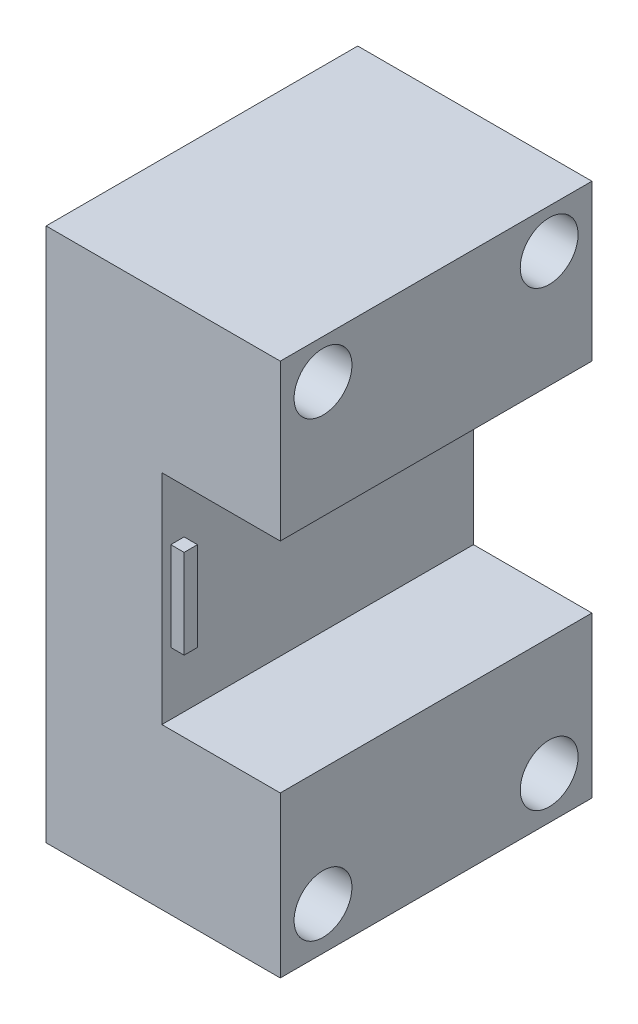
SolidWorks part; units mm, degrees
ref_plane "Front Plane" through (0, 0, 0) normal (0, 0, 1) x (1, 0, 0)
ref_plane "Top Plane" through (0, 0, 0) normal (0, 1, 0) x (1, 0, 0)
ref_plane "Right Plane" through (0, 0, 0) normal (1, 0, 0) x (0, 0, -1)
sketch "Sketch1" plane through (0, 0, 0) normal (0, 0, 1) x (1, 0, 0)
  line L0 (0, 0) -> (13, 0)
  line L7 (0, 60) -> (13, 60)
  line L9 (13, 60) -> (13, 0)
  line L10 (0, 60) -> (0, 0)
  point P4 (0, 0)
  point P6 (0, 0)
  dimension "D1" = 13
  dimension "D5" = 60
extrude "Boss-Extrude1" add sketch "Sketch1" against normal blind 35 contours L0 L9 L7 L10
sketch "Sketch3" plane through (13, 0, 0) normal (1, 0, 0) x (0, 0, -1)
  line L1 (1, 25) -> (2.5, 25)
  line L2 (1, 25) -> (1, 35)
  line L3 (1, 35) -> (2.5, 35)
  line L4 (2.5, 25) -> (2.5, 35)
  line L7 (0, 60) -> (0, 0) construction
  line L8 (35, 60) -> (0, 60) construction
  line L9 (35, 0) -> (0, 0) construction
  point P4 (8.1914, 30.5892)
  point P5 (15.7692, 27.331)
  point P8 (1.75, 35)
  dimension "D1" = 1.5
  dimension "D2" = 1
  dimension "D3" = 25
  dimension "D4" = 25
extrude "Boss-Extrude2" add sketch "Sketch3" along normal blind 1.5
sketch "Sketch7" plane through (0, 0, 0) normal (0, 0, 1) x (1, 0, 0)
  line L0 (13, 60) -> (26.3, 60)
  line L1 (26.3, 60) -> (26.3, 42.5)
  line L2 (26.3, 42.5) -> (13, 42.5)
  line L3 (13, 42.5) -> (13, 60)
  line L4 (13, 18) -> (26.3, 18)
  line L5 (26.3, 18) -> (26.3, 0)
  line L6 (26.3, 0) -> (13, 0)
  line L7 (13, 0) -> (13, 18)
  point P4 (0, 0)
  point P9 (0, 0)
  point P10 (0, 0)
  point P12 (0, 0)
  point P13 (0, 0)
  dimension "D1" = 13.3
  dimension "D2" = 17.5
  dimension "D3" = 18
  dimension "D4" = 13.3
extrude "Boss-Extrude6" add sketch "Sketch7" against normal up to surface (35 mm away) up to face at (6.5, 30, -35)
sketch "Sketch11" plane through (26.3, 0, 0) normal (1, 0, 0) x (0, 0, -1)
  line L0 (35, 0) -> (0, 0) construction
  line L1 (0, 0) -> (0, 18) construction
  line L2 (35, 18) -> (35, 0) construction
  circle A0 centre (4.8, 4.8) radius 3.25
  circle A1 centre (30.2, 4.8) radius 3.25
  circle A2 centre (30.2, 55.6) radius 3.25
  circle A3 centre (4.8, 55.6) radius 3.25
  point P8 (5.5004, 9.5777)
  point P9 (28.6621, 50.9619)
  point P10 (24.7437, 8.5935)
  point P11 (0, 0)
  point P12 (0, 0)
  point P13 (0, 0)
  point P20 (0, 0)
  point P22 (30.3315, 4.8016)
  dimension "D1" = 4.8
  dimension "D2" = 4.8
  dimension "D3" = 4.8
  dimension "D4" = 50.8
extrude "Cut-Extrude2" cut sketch "Sketch11" against normal through all
